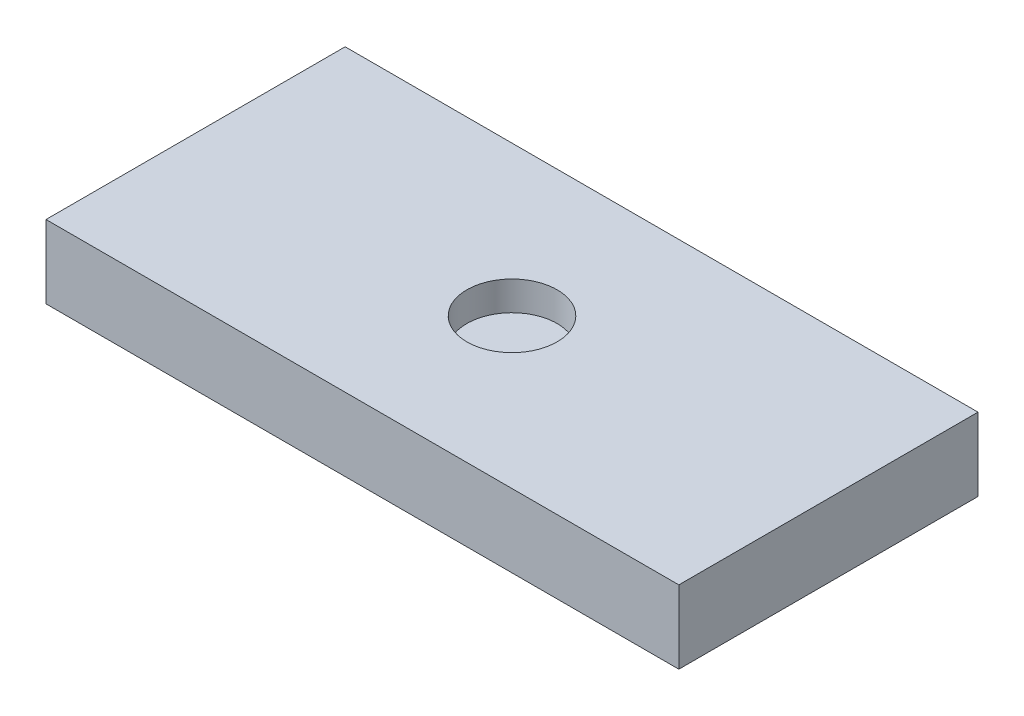
SolidWorks part; units mm, degrees
ref_plane "Front Plane" through (0, 0, 0) normal (0, 0, 1) x (1, 0, 0)
ref_plane "Top Plane" through (0, 0, 0) normal (0, 1, 0) x (1, 0, 0)
ref_plane "Right Plane" through (0, 0, 0) normal (1, 0, 0) x (0, 0, -1)
sketch "Sketch1" plane through (0, 0, 0) normal (0, 1, 0) x (1, 0, 0)
  line L1 (-27.5, -13) -> (27.5, -13)
  line L2 (-27.5, -13) -> (-27.5, 13)
  line L3 (-27.5, 13) -> (27.5, 13)
  line L4 (27.5, -13) -> (27.5, 13)
  line L5 (-27.5, -13) -> (27.5, 13) construction
  line L6 (-27.5, 13) -> (27.5, -13) construction
  point P0 (0, 0)
  dimension "D1" = 26
  dimension "D2" = 55
extrude "Boss-Extrude1" add sketch "Sketch1" along normal blind 6.35
sketch "Sketch2" plane through (0, 6.35, 0) normal (0, 1, 0) x (1, 0, 0)
  circle A0 centre (0, 0) radius 3.9232
extrude "Cut-Extrude1" cut sketch "Sketch2" against normal blind 2.54
